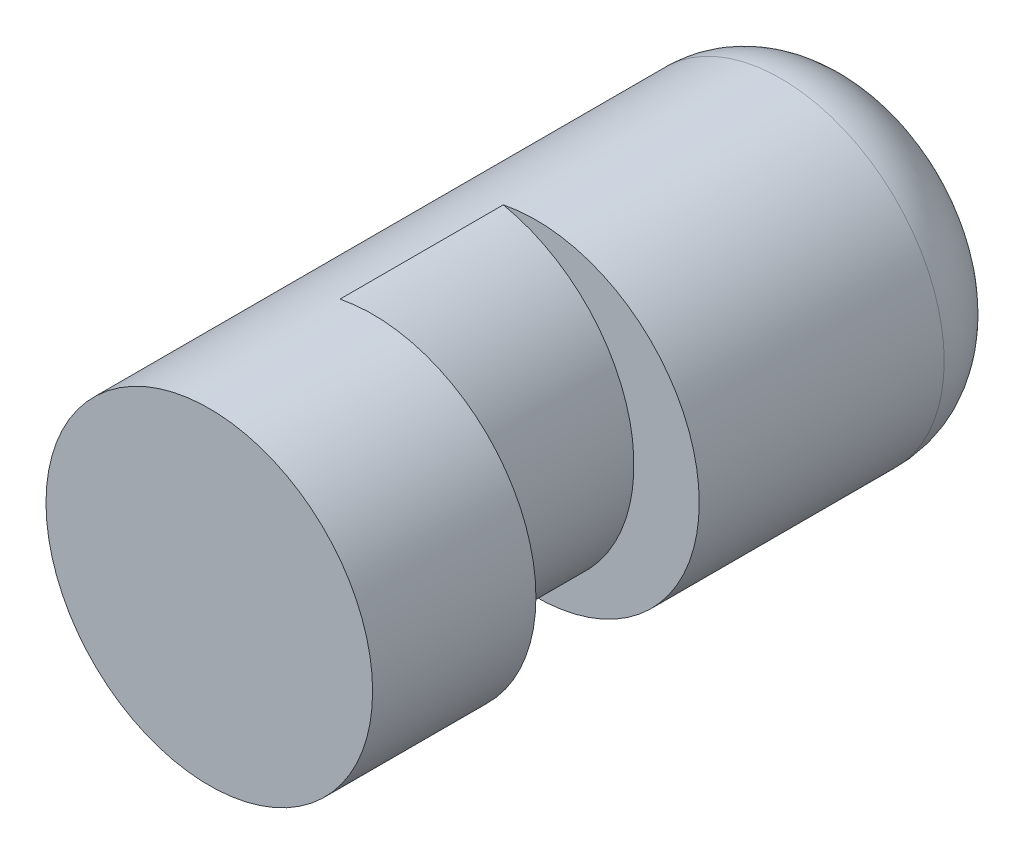
SolidWorks part; units mm, degrees
ref_plane "Front Plane" through (0, 0, 0) normal (0, 0, 1) x (1, 0, 0)
ref_plane "Top Plane" through (0, 0, 0) normal (0, 1, 0) x (1, 0, 0)
ref_plane "Right Plane" through (0, 0, 0) normal (1, 0, 0) x (0, 0, -1)
sketch "Sketch1" plane through (0, 0, 0) normal (0, 0, 1) x (1, 0, 0)
  circle A0 centre (-109.9089, 962.175) radius 6.35 construction
  circle A1 centre (-109.9089, 962.175) radius 6.35
extrude "Extrude1" add sketch "Sketch1" against normal blind 25.4
sketch "Sketch2" plane through (0, 0, -6.35) normal (0, 0, -1) x (-1, 0, 0)
  line L0 (112.4489, 962.175) -> (109.9089, 962.175) construction
  circle A0 centre (109.9089, 962.175) radius 6.35 construction
  circle A1 centre (109.9089, 962.175) radius 6.35 construction
  arc A2 (111.1789, 968.3967) -> (111.1789, 955.9533) centre (112.4489, 962.175) ccw
  arc A3 (111.1789, 968.3967) -> (111.1789, 955.9533) centre (109.9089, 962.175) ccw
  dimension "D1" = 2.54
extrude "Cut-Extrude1" cut sketch "Sketch2" along normal blind 6.35
fillet "Fillet1" radius 3.175 1 edges at (-103.5589, 962.175, -25.4)
sketch "Sketch3" plane through (0, 0, 0) normal (0, 0, 1) x (1, 0, 0)
  circle A1 centre (-109.9089, 962.175) radius 6.35
  circle A2 centre (-109.9089, 962.175) radius 6.35
  dimension "D1" = 0
extrude "Extrude2" [suppressed] add sketch "Sketch3" along normal blind 50.8
